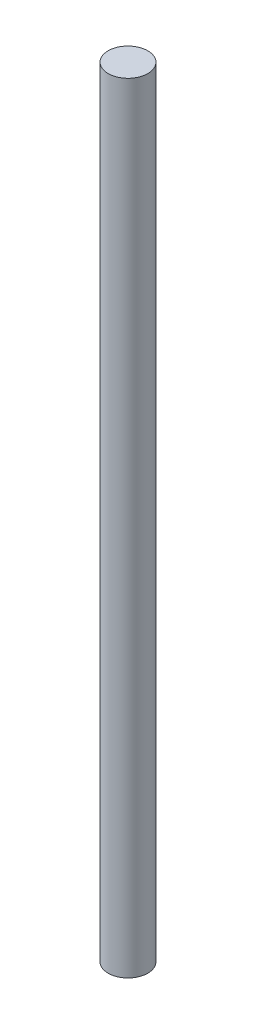
SolidWorks part; units mm, degrees
ref_plane "Front Plane" through (0, 0, 0) normal (0, 0, 1) x (1, 0, 0)
ref_plane "Top Plane" through (0, 0, 0) normal (0, 1, 0) x (1, 0, 0)
ref_plane "Right Plane" through (0, 0, 0) normal (1, 0, 0) x (0, 0, -1)
sketch "Sketch1" plane through (0, 0, 0) normal (0, 1, 0) x (1, 0, 0)
  circle A0 centre (0, 0) radius 1.935
  dimension "D1" = 3.87
extrude "Axle Body" add sketch "Sketch1" along normal blind 76.2
equation "\"CageLeftBottomEdge\"=22.11mm"
equation "\"CageLeftTopEdge\"=22.11mm"
equation "\"CageRightBottomEdge\"=21.63mm"
equation "\"CageRightTopEdge\"=21.63mm"
equation "\"CageHeight\"=86.04mm"
equation "\"CageLength\"=73.76mm"
equation "\"CageTopScrewClearance\"=10mm"
equation "\"CageBottomScrewClearance\"=25mm"
equation "\"CageLeftTopDepth\"= 11.65mm"
equation "\"CageLeftBottomDepth\"=11.11mm"
equation "\"CageLeftTopHeight\"=8.56175mm"
equation "\"CageLeftBottomHeight\"=16mm"
equation "\"CageRightTopDepth\"= 11.05mm"
equation "\"CageRightBottomDepth\"=10.58mm"
equation "\"CageRightTopHeight\"=9.6mm"
equation "\"CageRightBottomHeight\"=15.49mm"
equation "\"CageLeftTopChannelDepth\"=2.41908mm"
equation "\"CageLeftBottomChannelDepth\"=2.588mm"
equation "\"CageLeftChannelHeight\"=11.7mm"
equation "\"CageRightTopChannelDepth\"=2.32mm"
equation "\"CageRightBottomChannelDepth\"=2.318mm"
equation "\"CageRightChannelHeight\"=10mm"
equation "\"CageChanRelHeight\"=23.99mm"
equation "\"CageChanRelDepth\"=5.492mm"
equation "\"CageChamberRadius\"=16.261mm"
equation "\"CageScrewDiameter\"=4.8mm"
equation "\"CageSetScrewDiameter\"=3.5mm"
equation "\"CageAxleRadius\"=6.639mm"
equation "\"CageAxleKeyHeight\"=1.619mm"
equation "\"CageAxleKeyWidth\"=2.662mm"
equation "\"CageHoseWindowWidth\"=16.29mm"
equation "\"CageHoseWindowHeight\"=26.5mm"
equation "\"CageHoseWindow-Edge\"=8.89mm"
equation "\"CageScrew-VerticalEdge\"=5.0mm"
equation "\"CageScrew-HorizontalEdge\"=7.5mm"
equation "\"CageScrew-HoseCornerScrewEdge\"=4.45mm"
equation "\"CageAxle-BottomEdge\"=56.05mm"
equation "\"CageAxle-FrontEdge\"=46.03mm"
equation "\"CageBackSetScrew-Axle\"=40mm"
equation "\"CageFrontSetScrew-Axle\"=22mm"
equation "\"CageVelocityWindow-BackEdge\"=34.8mm"
equation "\"CageVelocityWindow-BottomEdge\"=27.55mm"
equation "\"CageVelocityWindowHeight\"=22.29mm"
equation "\"CageVelocityWindowWidth\"=12.61mm"
equation "\"TriggerSlot-BottomEdge\"=6.35mm"
equation "\"TriggerSlot-FrontEdge\"=15mm"
equation "\"TriggerSlotSize\"=6.7mm"
equation "\"TriggerRackOffset\"=6mm"
equation "\"TriggerSlotSizeInt\"=.25in"
equation "\"MotorMountLegLength\"=.25in"
equation "\"GearOffset\"=.264907in"
equation "\"TriggerSlotSpacing\"=.25in"
equation "\"TriggerMiniSlotWidth\"=3.5mm"
equation "\"TriggerRackWidth\"=6.5mm"
equation "\"pandiscradius\"=14in"
equation "\"towermaterialwidth\"=.25in"
equation "\"towerslotlength\"=.5in"
equation "\"towermarkerspace\"=5in"
equation "\"towerslothorizoffset\"=1in"
equation "\"towerslothorizspacing\"=2in"
equation "\"towerslotvertoffset\"=3in"
equation "\"towerslotvertspacing\"=1in"
equation "\"towerheight\"=12in"
equation "\"towerupslot\"=1in"
equation "\"toweraxle\"=.5in"
equation "\"stepperouterrad\"=10mm"
equation "\"stepperscrewsize\"=3.45mm"
equation "\"stepperscrewc2c\"=49.5mm"
equation "\"stepperdepthoffset\"=24mm"
equation "\"stepperhorizoffset\"=22.91mm"
equation "\"shaftslotOD\"=18.8mm"
equation "\"shaftslotID\"=13.28mm"
equation "\"shaftkeywidth\"=2.67mm"
equation "\"shaftkeydepth\"=1.8mm"
equation "\"shaftcollartotaldepth\"=12.5mm"
equation "\"shaftsquaredepth\"=6mm"
equation "\"shaftsetscrewsize\"=3.5mm"
equation "\"shaftkeytightdepth\"=1.85mm"
equation "\"shaftslottightID\"=12.78mm"
equation "\"shaftsetscrewoffset\"=9mm"
equation "\"cagecollartotaldepth\"=10mm"
equation "\"cagecollartotalwidth\"=35mm"
equation "\"cagecollarbasedepth\"=4mm"
equation "\"ajaxaxlesize\"=3.87mm"
equation "\"ajax4020gap\"=29.5mm"
equation "\"ajax4010gap\"=24.5mm"
equation "\"D1@Sketch1\"=\"ajaxaxlesize\""
equation "\"D1@Axle Body\"=\"towerslotvertspacing\"+\"towerslotlength\"+(6*\"towermaterialwidth\")"
equation "\"gearhubintdiam\"=30mm"
equation "\"gearhubintwid\"=15mm"
equation "\"towerspeedwidth\"=2in"
equation "\"towerspeedheight\"=8in"
equation "\"towerspeedgap\"=2in"
equation "\"stepperaxleflat\"=.037in"
equation "\"stepperaxlerad\"=0.11811024in"
equation "\"ajaxinnercut\"=2.3mm"
equation "\"ajaxwidth\"=6.1mm"
equation "\"ajaxdiametral\"=25.8854"
equation "\"ajaxcutoutdepth\"=2.3mm"
equation "\"ajax20hubbuffer\"=6.1mm"
equation "\"ajax20hubholeoffset\"=.19685in"
equation "\"ajax20hubholesize\"=.059055in"
equation "\"ajax20cutoutint\"=13.4mm"
equation "\"ajax40hubholesize\"=7.21mm"
equation "\"ajax40hubholeoffset\"=10mm"
equation "\"ajax40hubbuffer\"=8.9mm"
equation "\"ajax40cutoutint\"=32.6mm"
equation "\"bearingpandiscrad\"=6.8in"
equation "\"bearingpandiscang\"=48.75deg"
equation "\"bearingclearholedist\"=4.7345in"
equation "\"bearingclearholesize\"=.5in"
equation "\"bearingclearholeang\"=22.5deg"
equation "\"bearingmountholedist\"=4.25in"
equation "\"bearingwirehole\"=1.5in"
equation "\"no6diam\"=.146in"
equation "\"shortconangle\"=20deg"
equation "\"shortconlen\"=.875in"
equation "\"longconlen\"=1.25in"
equation "\"longconangle\"=15deg"
